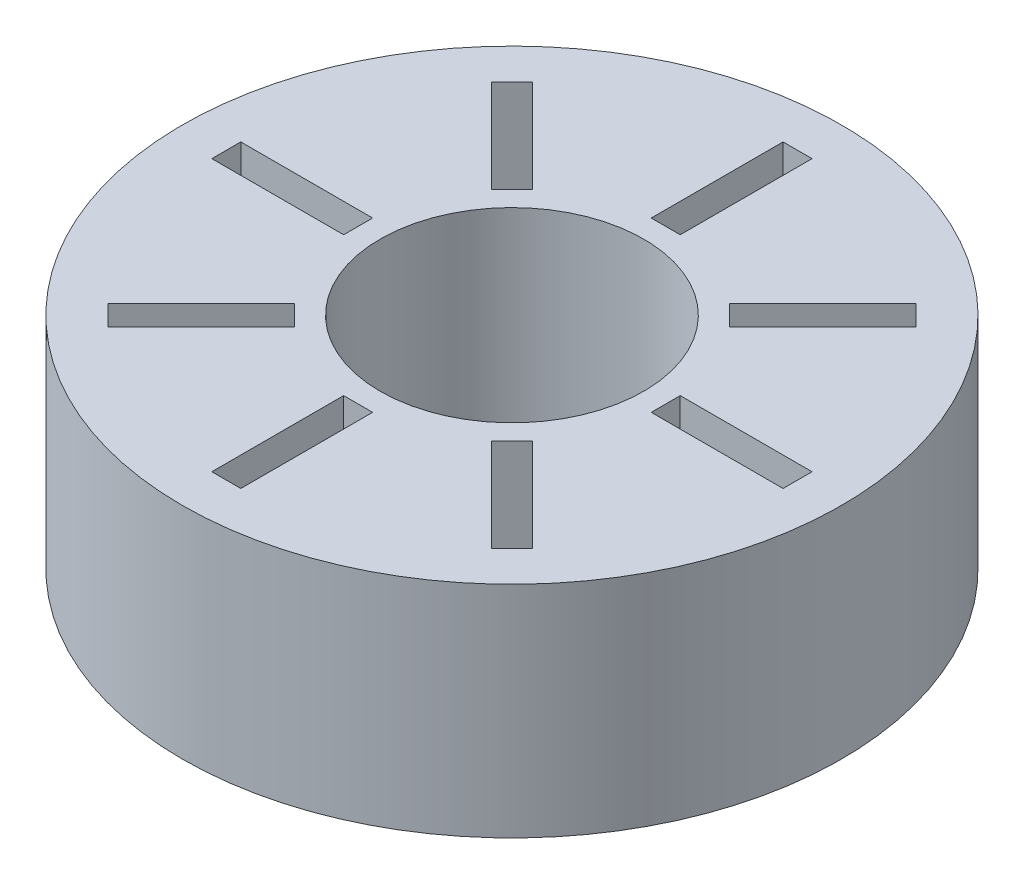
SolidWorks part; units mm, degrees
ref_plane "Спереди" through (0, 0, 0) normal (0, 0, 1) x (1, 0, 0)
ref_plane "Сверху" through (0, 0, 0) normal (0, 1, 0) x (1, 0, 0)
ref_plane "Справа" through (0, 0, 0) normal (1, 0, 0) x (0, 0, -1)
sketch "Эскиз1" plane through (0, 0, 0) normal (0, 1, 0) x (1, 0, 0)
  circle A0 centre (0, 0) radius 3
  circle A1 centre (0, 0) radius 7.5
  dimension "D1" = 6
  dimension "D2" = 15
extrude "Бобышка-Вытянуть1" add sketch "Эскиз1" along normal blind 5
sketch "Эскиз2" plane through (0, 5, 0) normal (0, 1, 0) x (1, 0, 0)
  line L1 (-0.3298, 6.5) -> (0.3298, 6.5)
  line L2 (-0.3298, 6.5) -> (-0.3298, 3.5)
  line L3 (-0.3298, 3.5) -> (0.3298, 3.5)
  line L4 (0.3298, 6.5) -> (0.3298, 3.5)
  line L5 (-0.3298, 6.5) -> (0.3298, 3.5) construction
  line L6 (-0.3298, 3.5) -> (0.3298, 6.5) construction
  circle A0 centre (0, 0) radius 3 construction
  circle A1 centre (0, 0) radius 7.5 construction
  point P0 (0, 5)
  point P53 (0, 0.6776)
  dimension "D1" = 3.5
  dimension "D2" = 6.5
extrude "Вырез-Вытянуть1" cut sketch "Эскиз2" against normal blind 10
pattern_circular "Круговой массив1" count 8 over 360 about axis through (0, 0, 0) along (0, 1, 0) of "Вырез-Вытянуть1"
